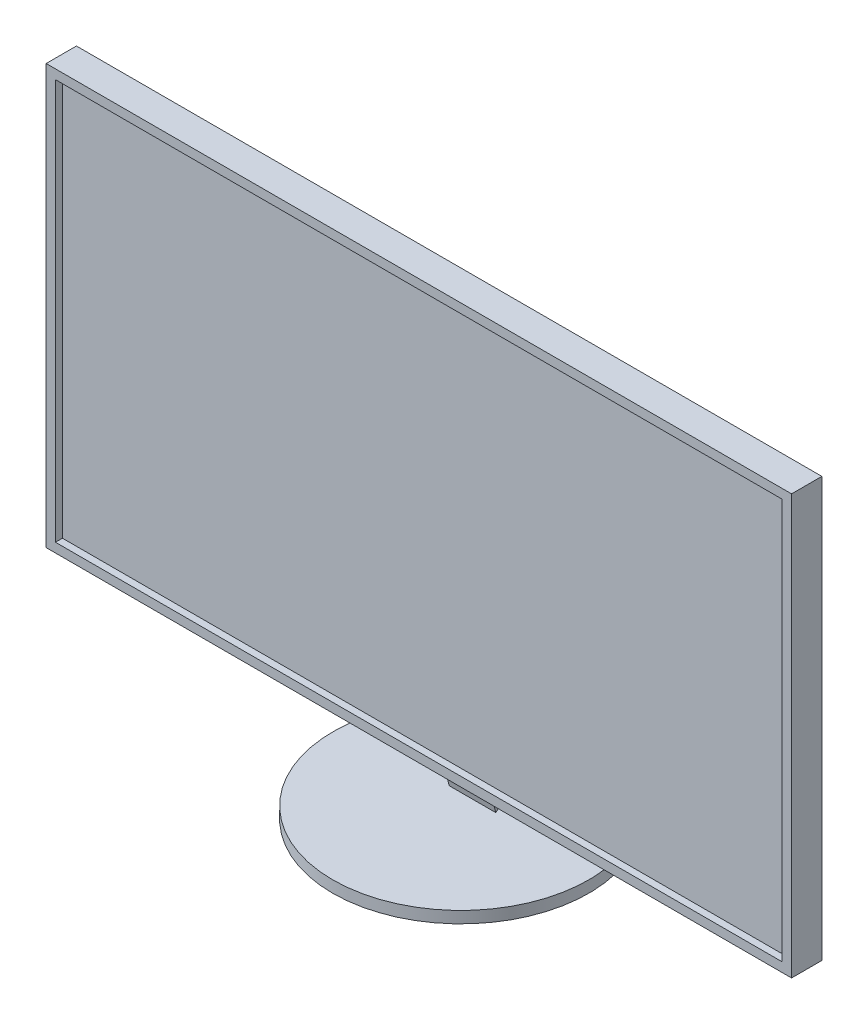
SolidWorks part; units mm, degrees
ref_plane "Front Plane" through (0, 0, 0) normal (0, 0, 1) x (1, 0, 0)
ref_plane "Top Plane" through (0, 0, 0) normal (0, 1, 0) x (1, 0, 0)
ref_plane "Right Plane" through (0, 0, 0) normal (1, 0, 0) x (0, 0, -1)
sketch "Sketch1" plane through (0, 0, 0) normal (0, 0, 1) x (1, 0, 0)
  line L1 (-80, 45) -> (80, 45)
  line L2 (-80, 45) -> (-80, -45)
  line L3 (-80, -45) -> (80, -45)
  line L4 (80, 45) -> (80, -45)
  line L5 (-80, 45) -> (80, -45) construction
  line L6 (-80, -45) -> (80, 45) construction
  point P0 (0, 0)
  dimension "D1" = 90
  dimension "D2" = 160
extrude "Boss-Extrude1" add sketch "Sketch1" along normal mid plane 5
sketch "Sketch2" plane through (0, 0, 2.5) normal (0, 0, 1) x (1, 0, 0)
  line L0 (80, -45) -> (80, 45) construction
  line L1 (-78, 43) -> (78, 43)
  line L2 (-78, 43) -> (-78, -43)
  line L3 (-78, -43) -> (78, -43)
  line L4 (78, 43) -> (78, -43)
  line L5 (-78, 43) -> (78, -43) construction
  line L6 (-78, -43) -> (78, 43) construction
  line L7 (-80, -45) -> (80, -45) construction
  line L9 (-80, -45) -> (80, -45)
  line L10 (-80, -45) -> (-80, 45)
  line L11 (-80, 45) -> (80, 45)
  line L12 (80, -45) -> (80, 45)
  line L13 (-80, -45) -> (80, 45) construction
  line L14 (-80, 45) -> (80, -45) construction
  point P0 (0, 0)
  point P10 (0, 0)
  dimension "D1" = 2
  dimension "D2" = 2
extrude "Boss-Extrude2" add sketch "Sketch2" along normal blind 1.5
ref_plane "Plane1" through (0, -60, 0) normal (0, 1, 0) x (1, 0, 0)
sketch "Sketch3" plane through (0, -60, 0) normal (0, 1, 0) x (1, 0, 0)
  circle A0 centre (0, 5) radius 27.5
  point P2 (0, 5)
  dimension "D2" = 55
  dimension "D1" = 5
extrude "Boss-Extrude3" add sketch "Sketch3" along normal blind 2.5 separate body
sketch "Sketch4" plane through (0, -57.5, 0) normal (0, 1, 0) x (1, 0, 0)
  line L0 (-5, 7.5) -> (0, 19.5)
  line L1 (0, 19.5) -> (5, 7.5)
  line L2 (5, 7.5) -> (-5, 7.5)
  line L3 (80, 2.5) -> (-80, 2.5) construction
  point P2 (0, 7.5)
  point P4 (5, 5.1804)
  point P8 (2.7061, 19.5)
  dimension "D1" = 10
  dimension "D2" = 12
  dimension "D3" = 5
sketch "Sketch5" plane through (0, 0, -2.5) normal (0, 0, -1) x (-1, 0, 0)
  line L0 (0, -22.5) -> (-5, -37.5)
  line L1 (-5, -37.5) -> (5, -37.5)
  line L2 (5, -37.5) -> (0, -22.5)
  line L3 (80, -45) -> (-80, -45) construction
  point P2 (0, -37.5)
  point P4 (0, 0)
  dimension "D1" = 15
  dimension "D2" = 10
  dimension "D3" = 7.5
loft "Loft1" add profiles "Sketch5", "Sketch4"
